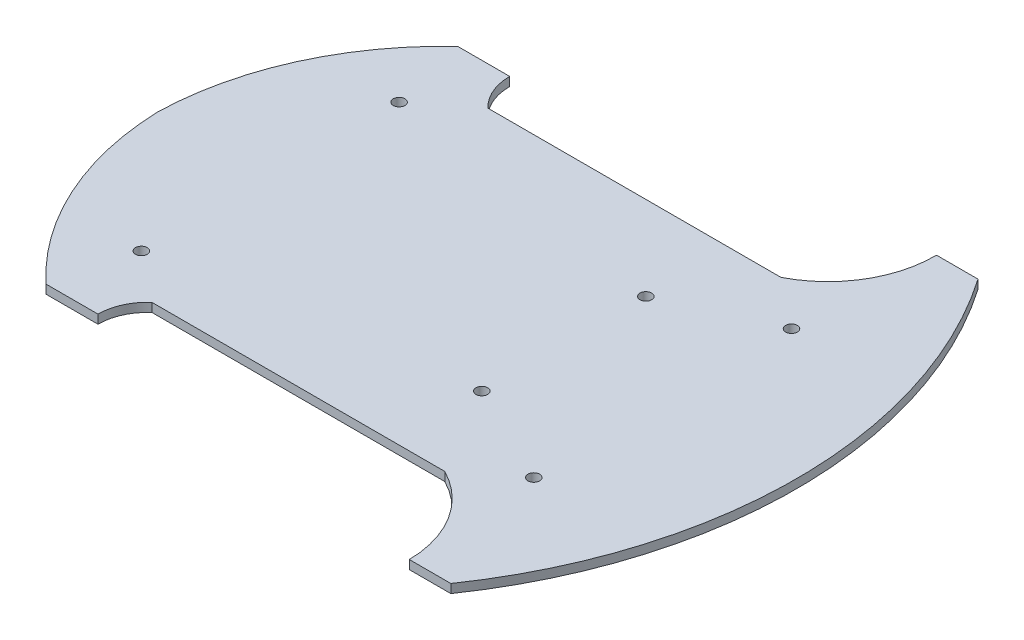
SolidWorks part; units mm, degrees
ref_plane "Front Plane" through (0, 0, 0) normal (0, 0, 1) x (1, 0, 0)
ref_plane "Top Plane" through (0, 0, 0) normal (0, 1, 0) x (1, 0, 0)
ref_plane "Right Plane" through (0, 0, 0) normal (1, 0, 0) x (0, 0, -1)
sketch "Sketch3" plane through (0, 0, 0) normal (0, 1, 0) x (1, 0, 0)
  line L5 (-49.171, 56.8777) -> (50.829, 56.8777)
  line L6 (-49.171, -57.8963) -> (50.829, -57.8963)
  line L7 (85, 90) -> (70.829, 90)
  line L8 (85, -90) -> (70.8254, -90)
  line L12 (33.4018, 28.179) -> (33.4018, -27.821)
  line L13 (-72.6123, 70) -> (-54.8938, 70)
  line L14 (100.829, -0.5093) -> (-195.5906, -0.5093) construction
  line L15 (-72.6123, -70.5826) -> (-54.8938, -70.5826)
  line L16 (-66.171, 43.4907) -> (67.829, 43.4907) construction
  line L17 (-66.171, 43.4907) -> (-66.171, -44.5093) construction
  line L23 (0.829, 56.8777) -> (0.829, -57.8963) construction
  line L24 (-72.6123, 70) -> (-72.6123, -70.5826) construction
  line L25 (-66.171, -44.5093) -> (67.829, -44.5093) construction
  line L26 (67.829, 43.4907) -> (67.829, -44.5093) construction
  line L27 (-66.171, 43.4907) -> (67.829, -44.5093) construction
  line L28 (-66.171, -44.5093) -> (67.829, 43.4907) construction
  line L29 (-54.8938, 70) -> (-54.8938, -70.5826) construction
  arc A0 (-108.6951, 57.8095) -> (-108.9057, 57.678) centre (-79.1436, 10.2509) ccw
  arc A1 (70.829, 90) -> (50.829, 56.8777) centre (34.2424, 89.4925) cw
  arc A2 (70.8254, -90) -> (50.829, -57.8963) centre (34.2388, -90.5093) ccw
  arc A3 (-54.8938, 70) -> (-49.171, 56.8777) centre (-36.9878, 70) ccw
  arc A4 (-54.8938, -70.5826) -> (-49.171, -57.8963) centre (-37.971, -70.5826) cw
  arc A5 (-108.6951, 57.8095) -> (-108.9057, 57.678) centre (-127.9193, 88.3611) cw
  circle A12 centre (33.4018, -27.821) radius 2
  arc A13 (-72.6123, -70.5826) -> (-104.4828, -0.5093) centre (-4.5332, 2.6652) cw
  arc A14 (-104.4828, -0.5093) -> (-72.6123, 70) centre (-4.52, -3.2354) cw
  circle A15 centre (33.4018, 28.179) radius 2
  circle A16 centre (-66.171, 43.4907) radius 2
  circle A17 centre (67.829, 43.4907) radius 2
  circle A18 centre (67.829, -44.5093) radius 2
  circle A19 centre (-66.171, -44.5093) radius 2
  arc A20 (85, 90) -> (85, -90) centre (-45.3861, 0) cw
  point P0 (0, 0)
  point P3 (0, 0)
  point P7 (104.9951, -90.4417)
  point P8 (104.9951, 89.5583)
  point P9 (100.829, 9.5239)
  point P12 (-88.713, 8.3612)
  point P19 (-90.2826, -79.9508)
  point P29 (-47.3808, -0.5093)
  point P41 (100.829, -0.5093)
  point P45 (0.829, -0.5093)
  point P55 (14.1088, 9.5239)
  point P74 (0.829, -0.5093)
  dimension "D4" = 88
  dimension "D9" = 56
  dimension "D14" = 4
  dimension "D1" = 180
  dimension "D3" = 20
  dimension "D15" = 134
  dimension "D16" = 100
  dimension "D7" = 20
  dimension "D8" = 20
  dimension "D10" = 20
extrude "Boss-Extrude3" add sketch "Sketch3" along normal blind 3 contours A16 | L8 A2 L6 A4 L15 A13 A14 L13 A3 L5 A1 L7 A20 | A18 | A17 | A19 | A12 | A15
